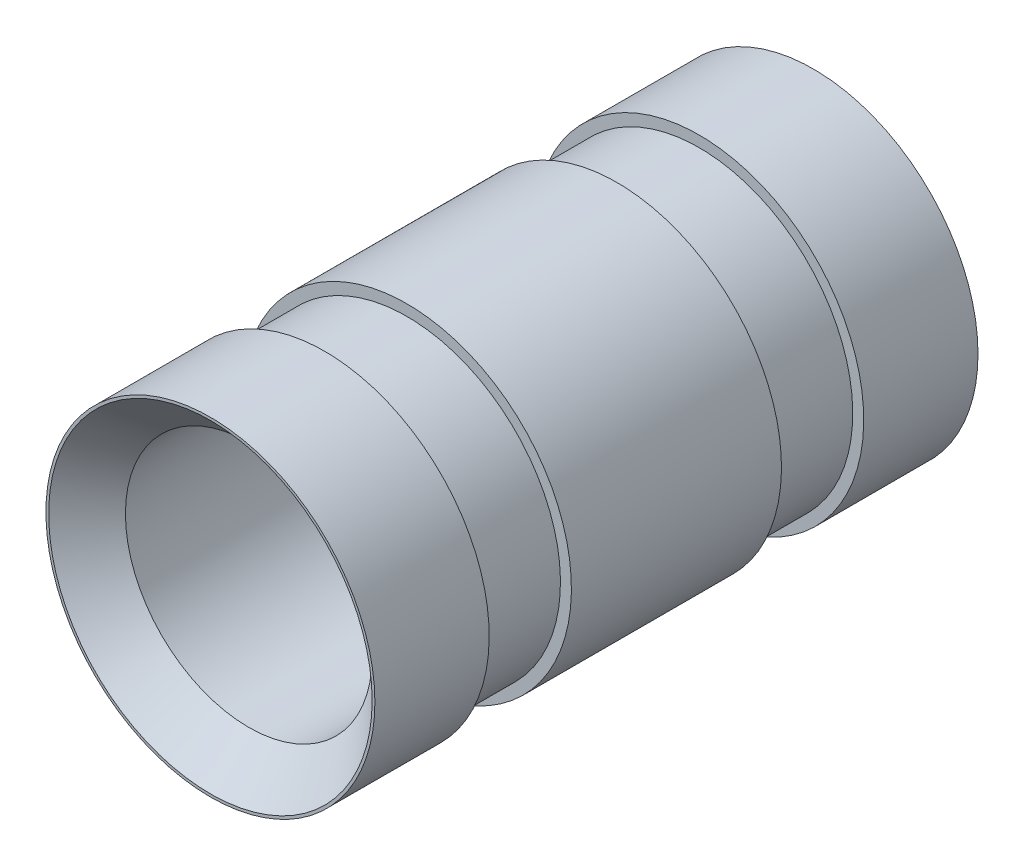
SolidWorks part; units mm, degrees
material "Cast Alloy Steel"
ref_plane "Front Plane" through (0, 0, 0) normal (0, 0, 1) x (1, 0, 0)
ref_plane "Top Plane" through (0, 0, 0) normal (0, 1, 0) x (1, 0, 0)
ref_plane "Right Plane" through (0, 0, 0) normal (1, 0, 0) x (0, 0, -1)
sketch "Sketch1" plane through (0, 0, 0) normal (0, 0, 1) x (1, 0, 0)
  line L0 (-38.1, 0) -> (38.1, 0) construction
  line L1 (0, -38.1) -> (0, 38.1) construction
  line L2 (0, 0) -> (0, 82.55) construction
  circle A0 centre (0, 0) radius 38.1
  circle A1 centre (0, 0) radius 28.575
  point P4 (0, 0)
  point P9 (0, 0)
  point P10 (28.575, 0)
  dimension "D1" = 57.15
  dimension "OD" = 76.2
  dimension "Wall Thickness" = 9.525
sketch "Sketch2" plane through (0, 0, 0) normal (1, 0, 0) x (0, 0, -1)
  line L0 (60.833, 38.1) -> (-60.833, 38.1) construction
  line L1 (0, 38.1) -> (0, -38.1) construction
  point P3 (26.797, 38.1)
  point P4 (0, 38.1)
  point P5 (-26.797, 38.1)
  dimension "D1" = 87.63
  dimension "D2" = 87.63
  dimension "Length" = 121.666
sketch "Sketch3" plane through (0, 0, 0) normal (0, 0, 1) x (1, 0, 0)
  line L0 (0, -38.1) -> (0, 38.1) construction
  circle A0 centre (0, 0) radius 38.1
  circle A1 centre (0, 0) radius 28.575
  circle A2 centre (0, 0) radius 28.575 construction
  dimension "D1" = 76.2
extrude "Boss-Extrude1" add sketch "Sketch3" along normal mid plane 139.7
sketch "Sketch4" plane through (0, 0, 0) normal (1, 0, 0) x (0, 0, -1)
  line L0 (-69.85, 38.1) -> (69.85, 38.1) construction
  line L1 (-69.85, 38.1) -> (-43.3789, 38.1)
  line L2 (-43.3789, 38.1) -> (-43.3789, 35.56)
  line L3 (-43.3789, 35.56) -> (-24.3289, 35.56)
  line L4 (-24.3289, 35.56) -> (-24.3289, 38.1)
  line L5 (-24.3289, 38.1) -> (24.3289, 38.1)
  line L6 (24.3289, 38.1) -> (24.3289, 35.56)
  line L7 (24.3289, 35.56) -> (43.3789, 35.56)
  line L8 (43.3789, 35.56) -> (43.3789, 38.1)
  line L9 (43.3789, 38.1) -> (69.85, 38.1)
  line L10 (-43.3789, 38.1) -> (-24.3289, 38.1)
  line L11 (24.3289, 38.1) -> (43.3789, 38.1)
  line L12 (0, 38.1) -> (0, 0) construction
  line L13 (-69.85, 0) -> (69.85, 0) construction
  line L14 (69.85, -28.575) -> (69.85, 28.575) construction
  line L15 (24.3289, 38.1) -> (43.3789, 38.1)
  line L16 (-43.3789, 38.1) -> (-24.3289, 38.1)
  point P20 (0, 0)
  dimension "D1" = 2.54
  dimension "D2" = 19.05
revolve "Cut-Revolve1" cut sketch "Sketch4" angle 360 about L13
chamfer "Chamfer1" distance 8.89 angle 45 1 edges at (28.575, 0, 69.85)
equation "\"D1@Boss-Extrude1\" = \"Length@Sketch2\""
equation "\"D1@Sketch2\"=\"OD@Sketch1\"*1.15"
equation "\"D2@Sketch2\"=\"D1@Sketch2\""
